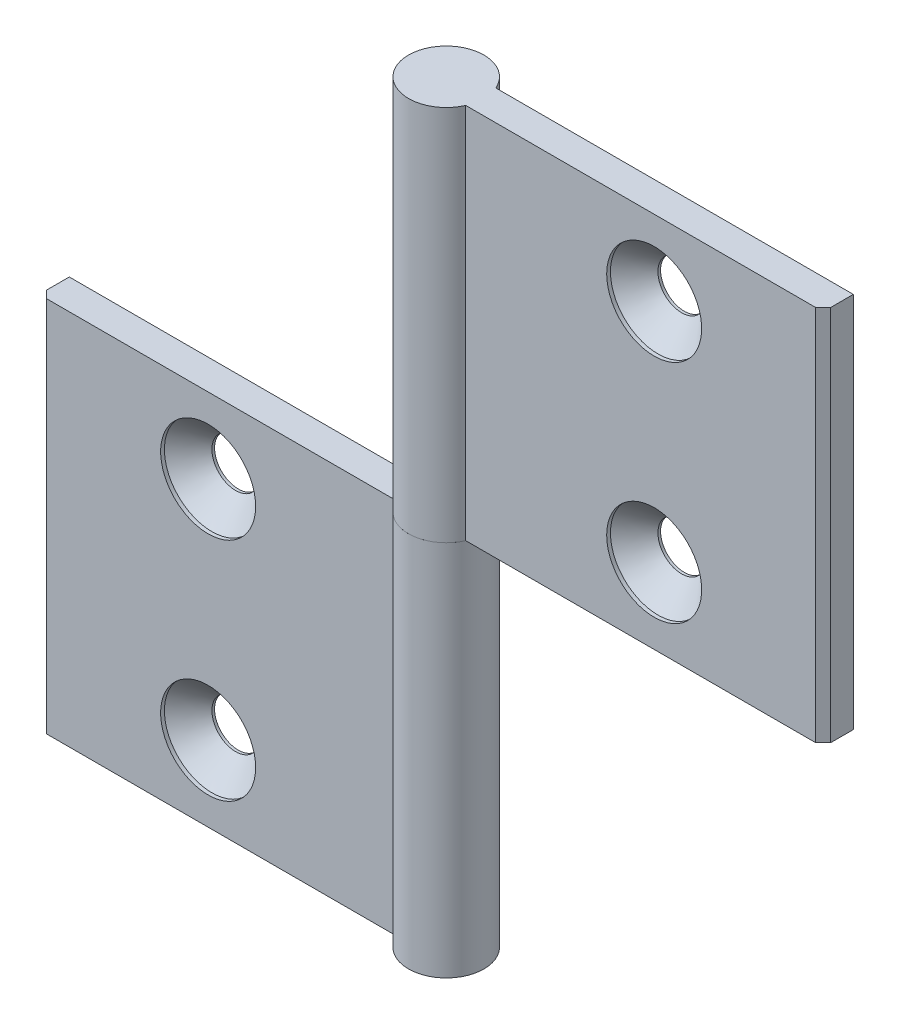
SolidWorks part; units mm, degrees
material "Алюминиевый сплав"
ref_plane "Спереди" through (0, 0, 0) normal (0, 0, 1) x (1, 0, 0)
ref_plane "Сверху" through (0, 0, 0) normal (0, 1, 0) x (1, 0, 0)
ref_plane "Справа" through (0, 0, 0) normal (1, 0, 0) x (0, 0, -1)
sketch "Эскиз1" plane through (0, 0, 0) normal (0, 1, 0) x (1, 0, 0)
  line L0 (-4.5826, 2) -> (-52, 2)
  line L1 (-52, 2) -> (-52, -1)
  line L2 (-52, -1) -> (-51, -2)
  line L3 (-51, -2) -> (-4.5826, -2)
  line L5 (-28.2913, 2) -> (-28.2913, -2) construction
  arc A0 (-4.5826, -2) -> (-4.5826, 2) centre (0, 0) ccw
  point P1 (-28.2913, 0)
  dimension "D5" = 5
  dimension "D1" = 47
  dimension "D2" = 4
  dimension "D3" = 3
  dimension "D4" = 45
extrude "Бобышка-Вытянуть1" add sketch "Эскиз1" along normal mid plane 50
hole_wizard "Зенковка для винта с полупотайной головкой M61" positions "Эскиз4" profile "Эскиз6" countersink size "M6" standard "ISO" end condition through all
sketch "Эскиз4" plane through (0, 0, 2) normal (0, 0, 1) x (1, 0, 0)
  line L0 (-29.5826, 15) -> (-29.5826, -15)
  line L2 (0.2087, -18.4577) -> (0.2087, 25) construction
  line L4 (5, 25) -> (-4.5826, 25) construction
  line L5 (-4.5826, 25) -> (-4.5826, -25) construction
  point P0 (-29.5826, 15)
  point P2 (-29.5826, -15)
  point P9 (-29.5826, 0)
  dimension "D1" = 30
  dimension "D2" = 25
sketch "Эскиз6" plane through (-29.5826, 15, 2) normal (1, 0, 0) x (0, -1, 0)
  line L0 (0, 0) -> (0, 7)
  line L1 (0, 7) -> (3.15, 7)
  line L2 (3.15, 7) -> (3.15, 3.65)
  line L3 (3.15, 3.65) -> (6.3, 0.5)
  line L4 (6.3, 0.5) -> (6.3, 0)
  line L6 (6.3, 0) -> (0, 0)
  line L7 (-3.15, 3.65) -> (-6.3, 0.5) construction
  line L11 (0, -6.35) -> (0, 107.95) construction
  dimension "Диаметр сквозного отверстия" = 6.3
  dimension "Глубина сквозного отверстия" = 7
  dimension "Диаметр зенковки" = 12.6
  dimension "Угол зенковки" = 90
  dimension "Утопленность" = 0.5
sketch "Угол раскрытия" plane through (0, 25, 0) normal (0, 1, 0) x (1, 0, 0)
  line L0 (0, 0) -> (0, -10)
  line L7 (-4.5826, 2) -> (-52, 2) construction
  dimension "D1" = 10
  dimension "D2" = 90
pattern_circular "Круговой массив1" count 2 over 360 about axis through (0, 25, 0) along (0, 0, 1) of bodies 106
